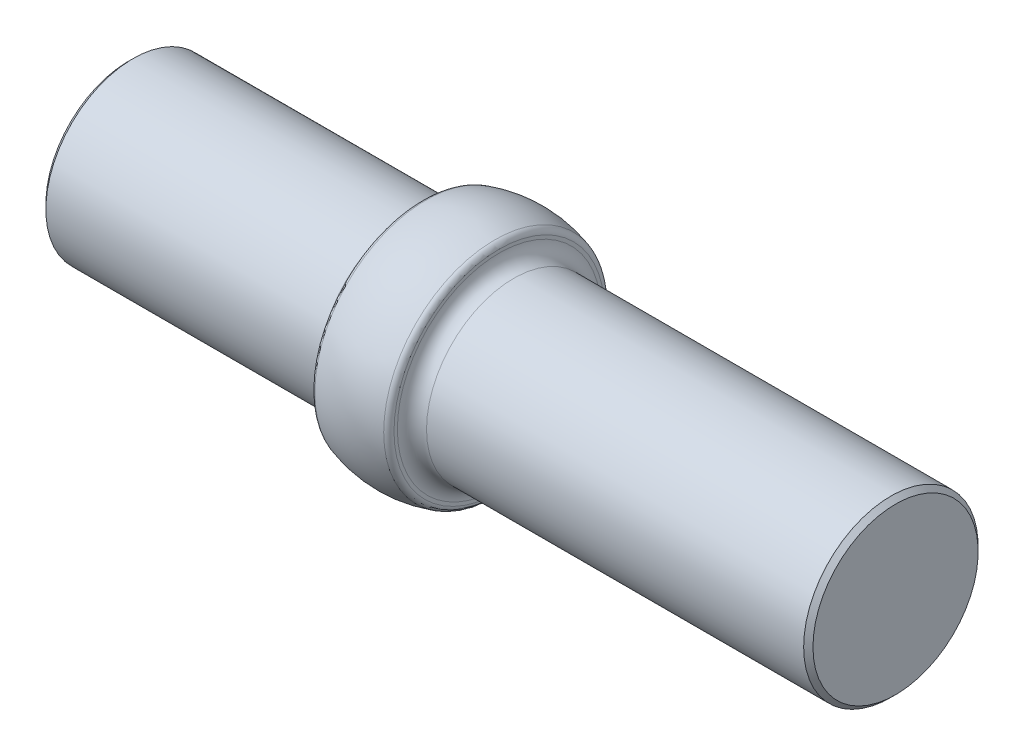
SolidWorks part; units mm, degrees
material "AISI 440C PER AMS 5630"
ref_plane "XY" through (0, 0, 0) normal (0, 0, 1) x (1, 0, 0)
ref_plane "XZ" through (0, 0, 0) normal (0, 1, 0) x (1, 0, 0)
ref_plane "YZ" through (0, 0, 0) normal (1, 0, 0) x (0, 0, -1)
sketch "Sketch1" plane through (0, 0, 0) normal (0, 0, 1) x (1, 0, 0)
  line L0 (0, 0) -> (90.5463, 0) construction
  line L1 (71.247, 14.2875) -> (71.247, 0)
  line L2 (71.247, 14.2875) -> (6.35, 14.2875)
  line L3 (0, 0) -> (0, -57.0585) construction
  line L4 (-54.356, 14.2875) -> (-6.35, 14.2875)
  line L5 (-54.356, 14.2875) -> (-54.356, 0)
  line L6 (71.247, 0) -> (-54.356, 0)
  line L9 (-6.35, 17.9605) -> (-6.35, 14.2875)
  line L10 (6.35, 17.9605) -> (6.35, 14.2875)
  arc A0 (-6.35, 17.9605) -> (6.35, 17.9605) centre (0, 0) cw
  point P16 (0, 19.05)
  dimension "D2" = 19.05
  dimension "D1" = 28.575
  dimension "D4" = 54.356
  dimension "D7" = 12.7
  dimension "D8" = 71.247
revolve "Revolve1" add sketch "Sketch1" angle 360 about L0
fillet "Fillet1" radius 2.3876 2 edges at (-6.35, 0, 14.2875) (6.35, 0, 14.2875)
chamfer "Chamfer1" distance 0.762 angle 45 2 edges at (71.247, 0, 14.2875) (-54.356, 0, 14.2875)
fillet "Fillet2" radius 1.016 2 edges at (6.35, 0, 17.9605) (-6.35, 0, 17.9605)
sketch "Sketch2" plane through (-54.356, 0, 0) normal (-1, 0, 0) x (0, 0, 1)
  line L0 (-11.3538, 1.016) -> (11.3538, 1.016) construction
  line L1 (0, 0) -> (0, 1.016) construction
  line L2 (-6.5909, 5.7658) -> (6.5909, 5.7658) construction
  line L3 (0, 1.016) -> (0, 5.7658) construction
  text T0 "D047935-V_" font "Century Gothic" height in points 10
  text T1 "OUT" font "Century Gothic" height in points 10
  dimension "D1" = 1.016
  dimension "D2" = 4.7498
extrude "Cut-Extrude1" cut sketch "Sketch2" against normal blind 0.0254
